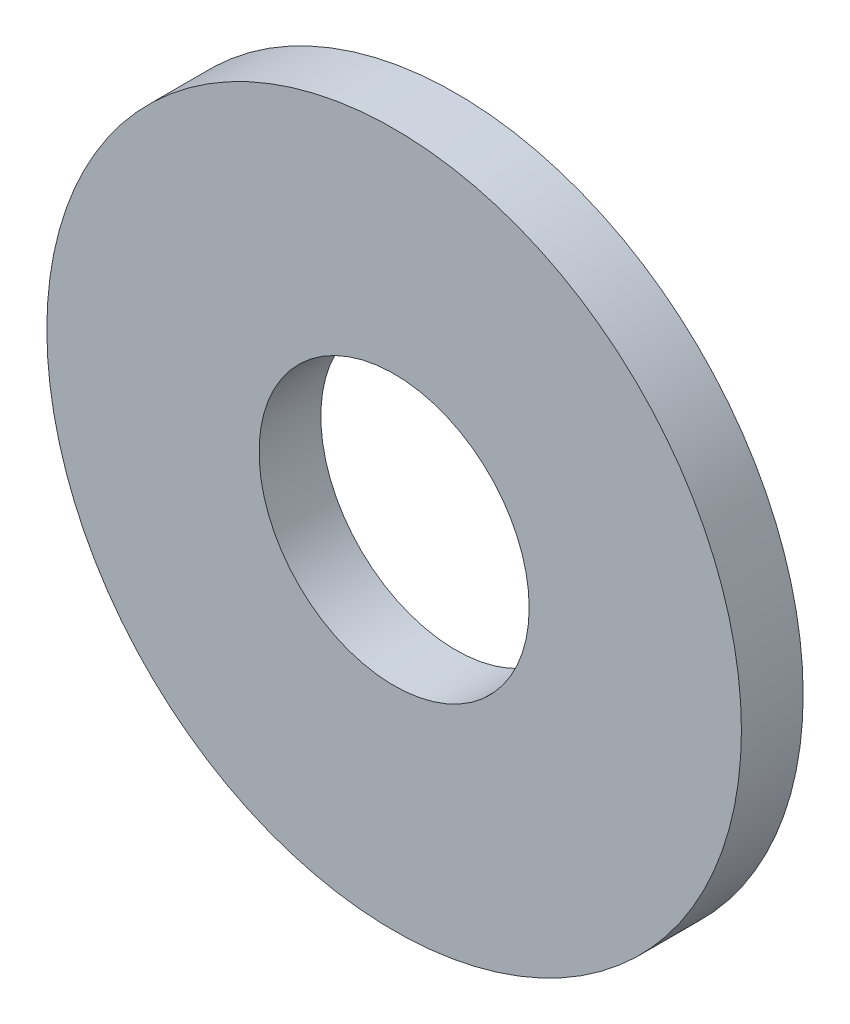
SolidWorks part; units mm, degrees
material "Acier allié"
ref_plane "Plan de face" through (0, 0, 0) normal (0, 0, 1) x (1, 0, 0)
ref_plane "Plan de dessus" through (0, 0, 0) normal (0, 1, 0) x (1, 0, 0)
ref_plane "Plan de droite" through (0, 0, 0) normal (1, 0, 0) x (0, 0, -1)
sketch "Esquisse1" plane through (0, 0, 0) normal (0, 0, 1) x (1, 0, 0)
  circle A0 centre (0, 0) radius 9
  circle A1 centre (0, 0) radius 3.5
  dimension "D1" = 7
  dimension "D2" = 18
extrude "Extrusion1" add sketch "Esquisse1" along normal blind 1.6
